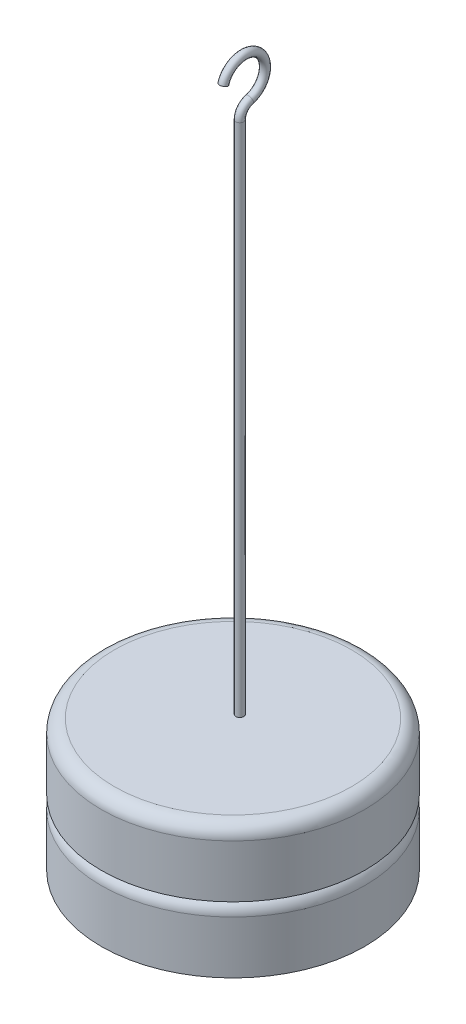
SolidWorks part; units mm, degrees
ref_plane "Front Plane" through (0, 0, 0) normal (0, 0, 1) x (1, 0, 0)
ref_plane "Top Plane" through (0, 0, 0) normal (0, 1, 0) x (1, 0, 0)
ref_plane "Right Plane" through (0, 0, 0) normal (1, 0, 0) x (0, 0, -1)
sketch "Sketch1" plane through (0, 0, 0) normal (0, 1, 0) x (1, 0, 0)
  circle A0 centre (0, 0) radius 12.7
  dimension "D1" = 25.4
extrude "Boss-Extrude1" add sketch "Sketch1" along normal blind 6.35
fillet "Fillet1" radius 1.27 1 edges at (0, 6.35, 12.7)
sketch "Sketch2" plane through (0, 6.35, 0) normal (0, 1, 0) x (1, 0, 0)
  circle A0 centre (0, 0) radius 12.7
  dimension "D1" = 25.4
extrude "Boss-Extrude2" add sketch "Sketch2" along normal blind 6.35
fillet "Fillet2" radius 1.27 1 edges at (0, 12.7, 12.7)
sketch "Sketch4" plane through (0, 0, 0) normal (1, 0, 0) x (0, 0, -1)
  line L6 (0.6539, 62.3355) -> (0.6539, 12.7)
  arc A3 (1.5836, 63.5591) -> (-0.9373, 66.0834) centre (1.0349, 65.532) ccw
  arc A5 (1.5836, 63.5591) -> (0.6539, 62.3355) centre (1.9239, 62.3355) ccw
  point P0 (0, 0)
  dimension "D5" = 1.27
sweep "Sweep1" add path "Sketch4" circular profile diameter 0.762 parameters "D3"=0.762
